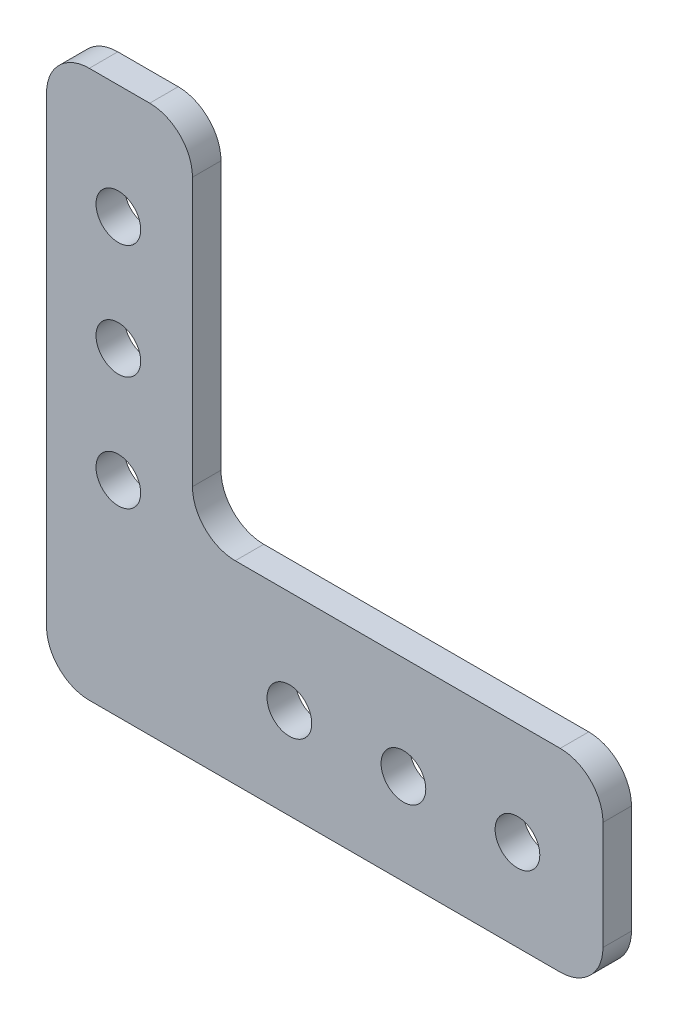
SolidWorks part; units mm, degrees
material "6061-T6 (SS)"
ref_plane "Front Plane" through (0, 0, 0) normal (0, 0, 1) x (1, 0, 0)
ref_plane "Top Plane" through (0, 0, 0) normal (0, 1, 0) x (1, 0, 0)
ref_plane "Right Plane" through (0, 0, 0) normal (1, 0, 0) x (0, 0, -1)
sketch "Sketch1" plane through (0, 0, 0) normal (0, 0, 1) x (1, 0, 0)
  line L1 (-34.925, -31.75) -> (34.925, -31.75)
  line L2 (-34.925, -31.75) -> (-34.925, 31.75)
  line L3 (-34.925, 31.75) -> (34.925, 31.75)
  line L4 (34.925, -31.75) -> (34.925, 31.75)
  line L5 (-34.925, -31.75) -> (34.925, 31.75) construction
  line L6 (-34.925, 31.75) -> (34.925, -31.75) construction
  line L7 (34.925, 31.75) -> (-10.795, 31.75)
  line L8 (34.925, 31.75) -> (34.925, -7.62)
  line L9 (34.925, -7.62) -> (-10.795, -7.62)
  line L10 (-10.795, 31.75) -> (-10.795, -7.62)
  line L11 (-34.925, -31.75) -> (-27.051, -31.75)
  line L12 (-34.925, -31.75) -> (-34.925, 31.75)
  line L13 (-34.925, 31.75) -> (-27.051, 31.75)
  line L14 (-27.051, -31.75) -> (-27.051, 31.75)
  line L15 (-27.051, -31.75) -> (34.925, -31.75)
  line L16 (-27.051, -31.75) -> (-27.051, -29.21)
  line L17 (-27.051, -29.21) -> (34.925, -29.21)
  line L18 (34.925, -31.75) -> (34.925, -29.21)
  circle A0 centre (-19.05, -19.05) radius 2.4892
  circle A1 centre (-19.05, -6.35) radius 2.4892
  circle A2 centre (-19.05, 6.35) radius 2.4892
  circle A3 centre (-19.05, 19.05) radius 2.4892
  circle A4 centre (0, -19.05) radius 2.4892
  circle A5 centre (12.7, -19.05) radius 2.4892
  circle A6 centre (25.4, -19.05) radius 2.4892
  point P0 (0, 0)
  dimension "D7" = 4.9784
  dimension "D1" = 69.85
  dimension "D2" = 63.5
  dimension "D3" = 24.13
  dimension "D4" = 24.13
  dimension "D5" = 7.874
  dimension "D6" = 63.5
  dimension "D8" = 15.875
  dimension "D9" = 12.7
  dimension "D10" = 12.7
  dimension "D11" = 12.7
  dimension "D12" = 12.7
  dimension "D13" = 12.7
  dimension "D14" = 27.051
  dimension "D15" = 12.7
  dimension "D16" = 2.54
extrude "Boss-Extrude1" add sketch "Sketch1" along normal blind 3.175 contours L14 L17 L4 L9 L10 L3 A6 A5 A4 A3 A2 A1 A0 | A0
fillet "Fillet1" radius 4.7625 6 edges at (-27.051, 31.75, 1.5875) (-10.795, 31.75, 1.5875) (-10.795, -7.62, 1.5875) (34.925, -7.62, 1.5875) (34.925, -29.21, 1.5875) (-27.051, -29.21, 1.5875)
